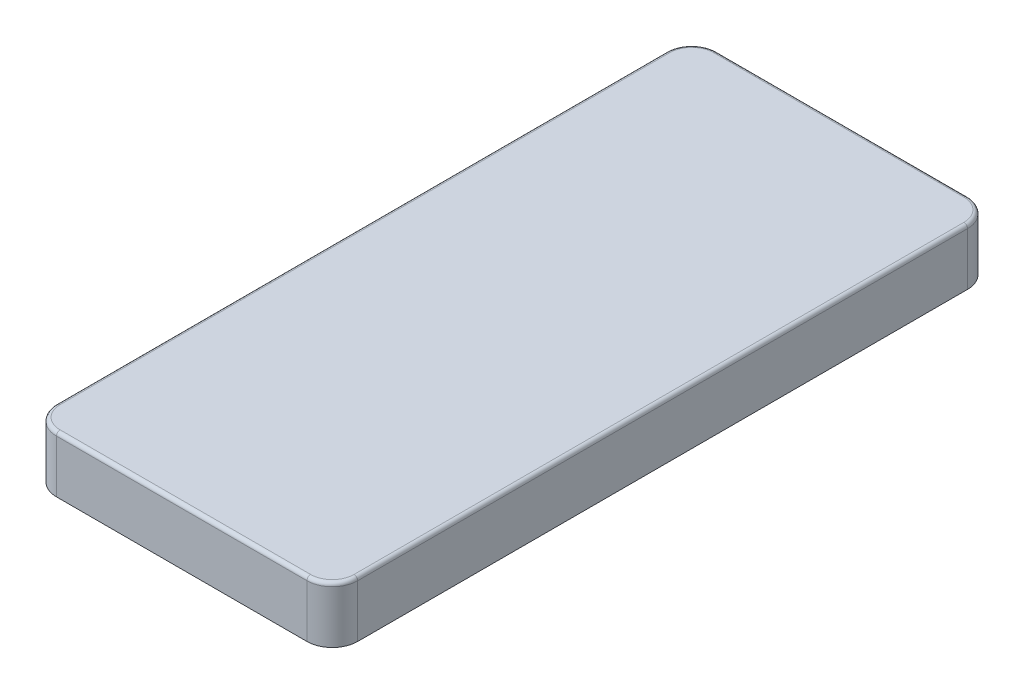
SolidWorks part; units mm, degrees
material "PP Кополимер"
ref_plane "Спереди" through (0, 0, 0) normal (0, 0, 1) x (1, 0, 0)
ref_plane "Сверху" through (0, 0, 0) normal (0, 1, 0) x (1, 0, 0)
ref_plane "Справа" through (0, 0, 0) normal (1, 0, 0) x (0, 0, -1)
sketch "Эскиз2" plane through (0, 0, 0) normal (0, 1, 0) x (1, 0, 0)
  line L1 (-7, 0) -> (-76, 0)
  line L2 (0, 7) -> (0, 175)
  line L3 (-7, 182) -> (-76, 182)
  line L4 (-83, 7) -> (-83, 175)
  arc A0 (-7, 0) -> (0, 7) centre (-7, 7) ccw
  arc A1 (-76, 0) -> (-83, 7) centre (-76, 7) cw
  arc A2 (-76, 182) -> (-83, 175) centre (-76, 175) ccw
  arc A3 (0, 175) -> (-7, 182) centre (-7, 175) ccw
  point P7 (0, 0)
  point P12 (-83, 182)
  point P15 (0, 182)
  dimension "D3" = 7
  dimension "D1" = 182
  dimension "D2" = 83
extrude "Бобышка-Вытянуть1" add sketch "Эскиз2" along normal blind 15.5
shell "Оболочка1" thickness 2
fillet "Скругление1" radius 1 8 edges at (-2.0503, 15.5, -2.0503) (-41.5, 15.5, 0) (-80.9497, 15.5, -2.0503) (-83, 15.5, -91) (-80.9497, 15.5, -179.9497) (-41.5, 15.5, -182) (-2.0503, 15.5, -179.9497) (0, 15.5, -91)
